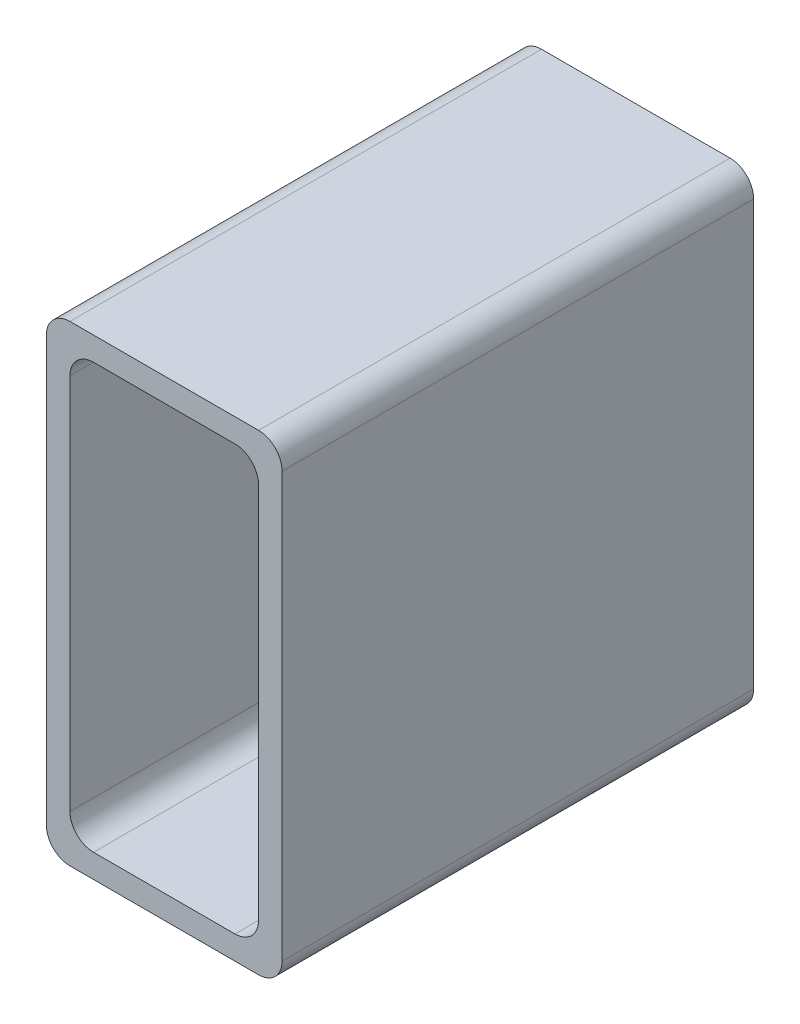
SolidWorks part; units mm, degrees
ref_plane "Płaszczyzna przednia" through (0, 0, 0) normal (0, 0, 1) x (1, 0, 0)
ref_plane "Płaszczyzna górna" through (0, 0, 0) normal (0, 1, 0) x (1, 0, 0)
ref_plane "Płaszczyzna prawa" through (0, 0, 0) normal (1, 0, 0) x (0, 0, -1)
sketch "Szkic1" plane through (0, 0, 0) normal (0, 0, 1) x (1, 0, 0)
  line L0 (-12, 27) -> (12, 27)
  line L1 (-12, -30) -> (12, -30)
  line L2 (-15, -27) -> (-15, 27)
  line L3 (-12, 30) -> (12, 30)
  line L4 (15, -27) -> (15, 27)
  line L5 (-15, -30) -> (15, 30) construction
  line L6 (-15, 30) -> (15, -30) construction
  line L7 (12, -27) -> (12, 27)
  line L8 (-12, -27) -> (12, -27)
  line L9 (-12, -27) -> (-12, 27)
  arc A0 (12, -30) -> (15, -27) centre (12, -27) ccw
  arc A1 (-12, -30) -> (-15, -27) centre (-12, -27) cw
  arc A2 (-15, 27) -> (-12, 30) centre (-12, 27) cw
  arc A3 (12, 30) -> (15, 27) centre (12, 27) cw
  arc A4 (12, 27) -> (12, 27) centre (12, 27) cw
  arc A5 (12, -27) -> (12, -27) centre (12, -27) ccw
  arc A6 (-12, -27) -> (-12, -27) centre (-12, -27) cw
  arc A7 (-12, 27) -> (-12, 27) centre (-12, 27) cw
  point P0 (0, 0)
  dimension "D3" = 3
  dimension "D1" = 60
  dimension "D2" = 30
  dimension "D4" = 3
extrude "Dodanie-wyciągnięcie1" add sketch "Szkic1" along normal blind 60
fillet "Zaokrąglenie1" radius 3 4 edges at (12, -27, 30) (12, 27, 30) (-12, 27, 30) (-12, -27, 30)
